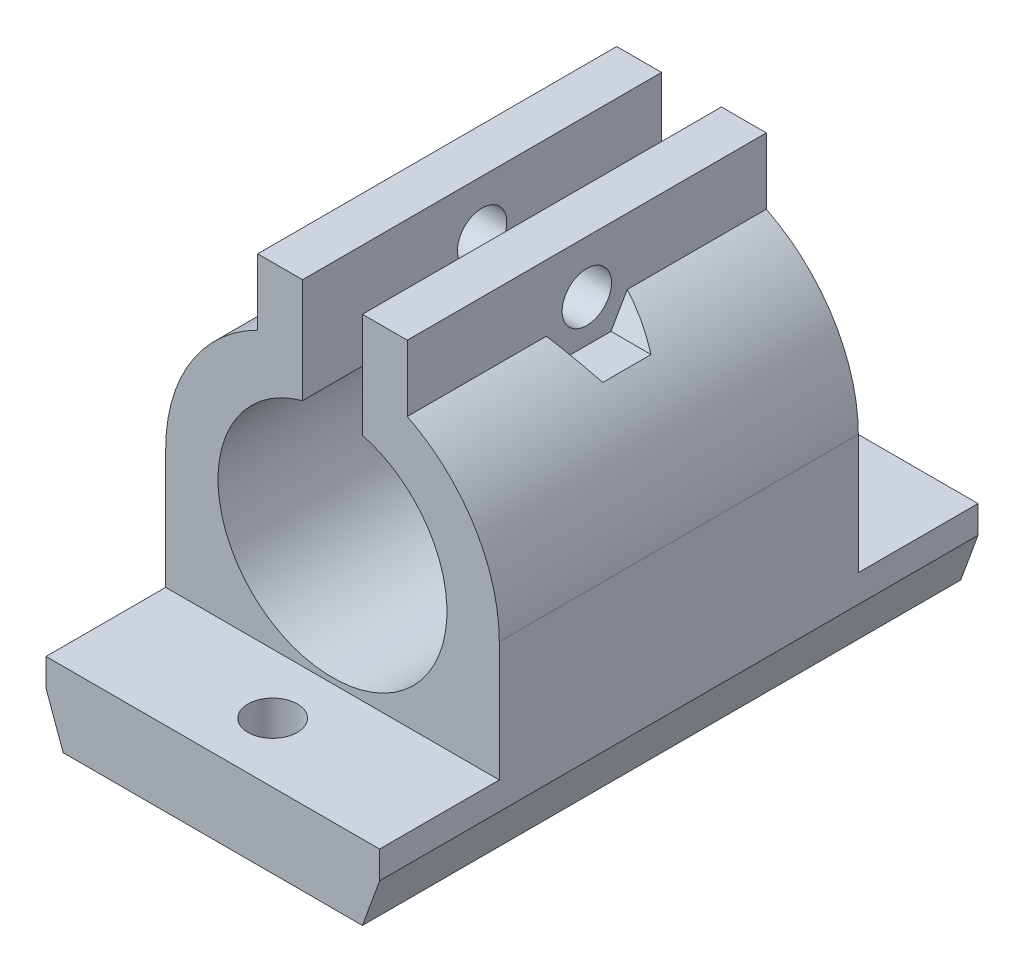
SolidWorks part; units mm, degrees
ref_plane "Plano frontal" through (0, 0, 0) normal (0, 0, 1) x (1, 0, 0)
ref_plane "Plano superior" through (0, 0, 0) normal (0, 1, 0) x (1, 0, 0)
ref_plane "Plano direito" through (0, 0, 0) normal (1, 0, 0) x (0, 0, -1)
sketch "Esboço1" plane through (0, 0, 0) normal (0, 0, 1) x (1, 0, 0)
  line L0 (5, 14.3839) -> (5, 9.9661)
  line L1 (11.15, -13) -> (-11.15, -13)
  line L2 (-11.15, -13) -> (-11.15, 0)
  line L3 (-2, 7.3839) -> (-2, 14.3839)
  line L4 (-2, 14.3839) -> (-5, 14.3839)
  line L5 (-5, 14.3839) -> (-5, 9.9661)
  line L6 (0, 19.1253) -> (0, 0) construction
  line L7 (2, 14.3839) -> (5, 14.3839)
  line L8 (2, 7.3839) -> (2, 14.3839)
  line L9 (11.15, -13) -> (11.15, 0)
  arc A0 (-5, 9.9661) -> (-11.15, 0) centre (0, 0) ccw
  arc A1 (-2, 7.3839) -> (2, 7.3839) centre (0, 0) ccw
  arc A2 (5, 9.9661) -> (11.15, 0) centre (0, 0) cw
  point P3 (0, 0)
  point P17 (0, -13)
  dimension "D1" = 15.3
  dimension "D2" = 3.5
  dimension "D3" = 4
  dimension "D4" = 3
  dimension "D5" = 7
  dimension "D6" = 13
  dimension "D7" = 14.3839
extrude "Ressalto-extrusão1" add sketch "Esboço1" along normal blind 40
sketch "Esboço2" plane through (0, 14.3839, 0) normal (0, 1, 0) x (1, 0, 0)
  line L0 (11.15, -40) -> (11.15, 0) construction
  line L1 (-11.15, -32) -> (11.15, -32)
  line L2 (0, -20) -> (13.9851, -20) construction
  line L3 (-11.15, -8) -> (11.15, -8)
  line L7 (-2, -40) -> (-2, 0) construction
  line L8 (-11.15, -40) -> (-11.15, 0) construction
  line L9 (-11.15, -32) -> (-11.15, -40)
  line L10 (-11.15, 0) -> (11.15, 0)
  line L11 (-11.15, 0) -> (-11.15, -8)
  line L12 (-11.15, -40) -> (11.15, -40)
  line L13 (11.15, 0) -> (11.15, -8)
  line L14 (11.15, -32) -> (11.15, -40)
  point P0 (0, -20)
  point P8 (-2, -20)
  dimension "D1" = 24
extrude "Corte-extrusão1" cut sketch "Esboço2" against normal offset from surface (22.3839 mm away) 5 up to face at (0, -13, 20)
sketch "Esboço3" plane through (0, -8, 0) normal (0, 1, 0) x (1, 0, 0)
  line L0 (11.15, -8) -> (-11.15, -8) construction
  line L1 (-11.15, -20) -> (16.8976, -20) construction
  line L2 (-11.15, -32) -> (-11.15, -8) construction
  circle A0 centre (0, -4) radius 1.65
  circle A1 centre (0, -36) radius 1.65
  dimension "D1" = 3.3
  dimension "D2" = 4
extrude "Corte-extrusão2" cut sketch "Esboço3" against normal blind 5
sketch "Esboço4" plane through (-5, 0, 0) normal (-1, 0, 0) x (0, 0, 1)
  line L0 (32, 7.3839) -> (8, 7.3839) construction
  line L1 (40, -13) -> (0, -13) construction
  circle A0 centre (20, 10.8839) radius 1.65
  circle A1 centre (20, 10.8839) radius 3.5 construction
  point P6 (20, -13)
  dimension "D1" = 3.3
  dimension "D2" = 7
extrude "Corte-extrusão3" cut sketch "Esboço4" against normal through all both and the other way through all
sketch "Esboço5" plane through (-5, 0, 0) normal (-1, 0, 0) x (0, 0, 1)
  circle A0 centre (20, 10.8839) radius 3.5
extrude "Corte-extrusão4" cut sketch "Esboço5" along normal blind 10
sketch "Esboço6" plane through (5, 0, 0) normal (1, 0, 0) x (0, 0, -1)
  line L1 (-16.7668, 10.8839) -> (-18.3834, 13.6839)
  line L2 (-18.3834, 13.6839) -> (-21.6166, 13.6839)
  line L3 (-21.6166, 13.6839) -> (-23.2332, 10.8839)
  line L4 (-23.2332, 10.8839) -> (-21.6166, 8.0839)
  line L5 (-21.6166, 8.0839) -> (-18.3834, 8.0839)
  line L6 (-18.3834, 8.0839) -> (-16.7668, 10.8839)
  circle A0 centre (-20, 10.8839) radius 2.8 construction
  dimension "D1" = 5.6
extrude "Corte-extrusão5" cut sketch "Esboço6" along normal blind 10
chamfer "Chanfro1" distance 1.15 angle 70 2 edges at (11.15, -13, 20) (-11.15, -13, 20)
ref_plane "Plano1" through (-5, 14.3839, 32) normal (-1, 0, 0) x (0, 0, 1)
